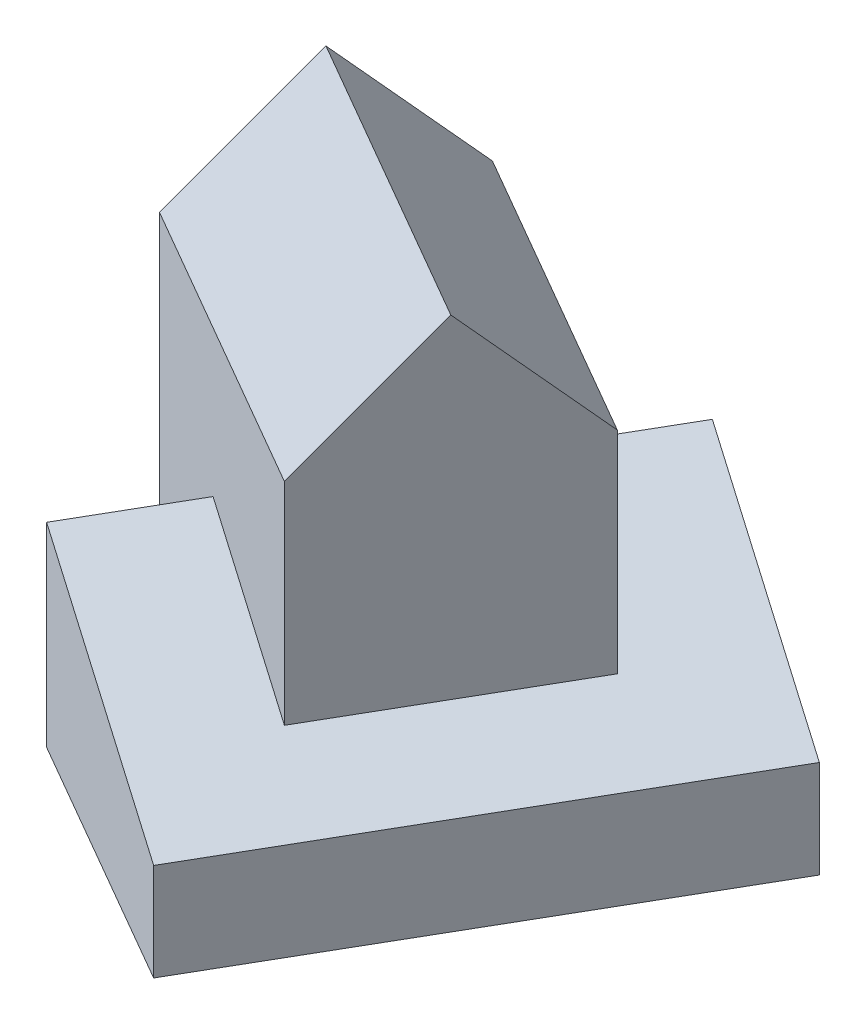
SolidWorks part; units mm, degrees
other "Perspective"
ref_plane "Front" through (0, 0, 0) normal (0, 0, 1) x (1, 0, 0)
ref_plane "Top" through (0, 0, 0) normal (0, 1, 0) x (1, 0, 0)
ref_plane "Right" through (0, 0, 0) normal (1, 0, 0) x (0, 0, -1)
sketch "Sketch1" plane through (0, 0, 0) normal (0, 1, 0) x (1, 0, 0)
  line L1 (0, 0) -> (50, 86.6025)
  line L2 (50, 86.6025) -> (-1.9615, 116.6025)
  line L3 (0, 0) -> (-51.9615, 30)
  line L4 (-1.9615, 116.6025) -> (-51.9615, 30)
  dimension "D2" = 60
  dimension "D3" = 60
  dimension "D4" = 100
extrude "Extrude1" add sketch "Sketch1" along normal blind 40
sketch "Sketch2" plane through (0, 0, 0) normal (-0.5, 0, 0.866) x (0.866, 0, 0.5)
  line L2 (0, 40) -> (0, 0) construction
  line L3 (0, 20) -> (-60, 40)
  line L5 (-60, 40) -> (0, 40)
  line L6 (0, 40) -> (0, 20)
extrude "Cut-Extrude1" cut sketch "Sketch2" against normal through all
sketch "Sketch3" plane through (0, 0, 0) normal (0, 1, 0) x (1, 0, 0)
  line L3 (-65.4423, 66.6506) -> (-40.4423, 109.9519)
  line L4 (-4.8205, 31.6506) -> (20.1795, 74.9519)
  line L5 (20.1795, 74.9519) -> (-40.4423, 109.9519)
  line L6 (-4.8205, 31.6506) -> (-65.4423, 66.6506)
extrude "Extrude2" add sketch "Sketch3" along normal blind 70
sketch "Sketch4" plane through (-17.3205, 0, -10) normal (0.866, 0, 0.5) x (0.5, 0, -0.866)
  line L0 (25, 70) -> (75, 70)
  line L2 (25, 70) -> (50, 95)
  line L3 (50, 95) -> (75, 70)
extrude "Extrude3" add sketch "Sketch4" against normal blind 70
